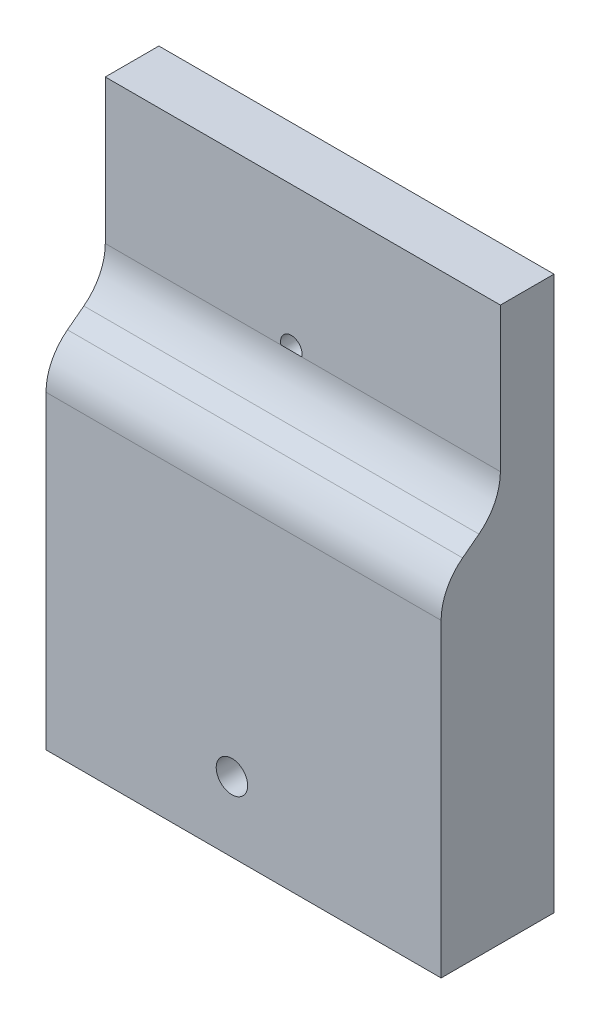
SolidWorks part; units mm, degrees
ref_plane "Front Plane" through (0, 0, 0) normal (0, 0, 1) x (1, 0, 0)
ref_plane "Top Plane" through (0, 0, 0) normal (0, 1, 0) x (1, 0, 0)
ref_plane "Right Plane" through (0, 0, 0) normal (1, 0, 0) x (0, 0, -1)
sketch "Sketch1" plane through (0, 0, 0) normal (0, 0, 1) x (1, 0, 0)
  line L1 (-110.6575, 3.089) -> (-47.1575, 3.089)
  line L2 (-110.6575, 3.089) -> (-110.6575, 91.989)
  line L3 (-110.6575, 91.989) -> (-47.1575, 91.989)
  line L4 (-47.1575, 3.089) -> (-47.1575, 91.989)
  dimension "D1" = 88.9
  dimension "D2" = 63.5
extrude "Boss-Extrude1" add sketch "Sketch1" along normal up to surface (18.1387 mm away)
sketch "Sketch2" plane through (-110.6575, 0, 0) normal (-1, 0, 0) x (0, 0, 1)
  line L0 (8.6137, 74.0185) -> (8.6137, 69.2433) construction
  line L1 (8.6137, 69.2433) -> (8.6137, 68.8056) construction
  line L2 (12.0626, 61.8377) -> (13.078, 61.0633) construction
  line L3 (13.078, 61.0633) -> (13.6744, 60.6085) construction
  line L4 (13.6744, 60.6085) -> (14.6898, 59.834) construction
  line L5 (18.1387, 14.3158) -> (18.1387, 52.8662) construction
  line L6 (8.6137, 74.0185) -> (8.6137, 69.2433)
  line L7 (8.6137, 69.2433) -> (8.6137, 68.8056)
  line L8 (12.0626, 61.8377) -> (13.078, 61.0633)
  line L9 (13.078, 61.0633) -> (13.6744, 60.6085)
  line L10 (13.6744, 60.6085) -> (14.6898, 59.834)
  line L11 (18.1387, 14.3158) -> (18.1387, 52.8662)
  line L12 (8.6137, 74.0185) -> (8.6137, 91.989)
  line L13 (18.1387, 91.989) -> (0, 91.989) construction
  line L14 (8.6137, 91.989) -> (18.1387, 91.989)
  line L15 (18.1387, 91.989) -> (18.1387, 52.8662)
  arc A0 (8.6358, 68.1839) -> (12.0626, 61.8377) centre (17.3767, 68.8056) ccw construction
  arc A1 (8.6137, 68.8056) -> (8.6358, 68.1839) centre (17.3767, 68.8056) ccw construction
  arc A2 (18.1166, 53.4879) -> (14.6898, 59.834) centre (9.3757, 52.8662) ccw construction
  arc A3 (18.1387, 52.8662) -> (18.1166, 53.4879) centre (9.3757, 52.8662) ccw construction
  arc A4 (8.6358, 68.1839) -> (12.0626, 61.8377) centre (17.3767, 68.8056) ccw
  arc A5 (8.6137, 68.8056) -> (8.6358, 68.1839) centre (17.3767, 68.8056) ccw
  arc A6 (18.1166, 53.4879) -> (14.6898, 59.834) centre (9.3757, 52.8662) ccw
  arc A7 (18.1387, 52.8662) -> (18.1166, 53.4879) centre (9.3757, 52.8662) ccw
extrude "Cut-Extrude1" cut sketch "Sketch2" against normal up to surface (63.5 mm away) contours A7 L12 L6 L7 A5 A4 L8 L9 L10 A6 M2 M3 up to face at (-47.1575, 47.539, 9.0693)
sketch3d "Sketch_MAC1-1_PART1_MILLING" [suppressed]
  line L0 (-47.1575, 3.089, 18.1387) -> (-47.1575, 13.089, 18.1387)
  line L1 (-47.1575, 3.089, 18.1387) -> (-57.1575, 3.089, 18.1387)
  point P0 (-47.1575, 3.089, 18.1387)
  point P1 (-47.1575, 13.089, 18.1387)
  point P2 (-57.1575, 3.089, 18.1387)
sketch3d "Stock_PART1_MILLING"
  line L12 (-47.1575, 3.089, 0) -> (-47.1575, 91.989, 0)
  line L13 (-47.1575, 91.989, 0) -> (-110.6575, 91.989, 0)
  line L14 (-110.6575, 91.989, 0) -> (-110.6575, 3.089, 0)
  line L15 (-110.6575, 3.089, 0) -> (-47.1575, 3.089, 0)
  line L16 (-47.1575, 3.089, 18.1387) -> (-47.1575, 91.989, 18.1387)
  line L17 (-47.1575, 91.989, 18.1387) -> (-110.6575, 91.989, 18.1387)
  line L18 (-110.6575, 91.989, 18.1387) -> (-110.6575, 3.089, 18.1387)
  line L19 (-110.6575, 3.089, 18.1387) -> (-47.1575, 3.089, 18.1387)
  line L20 (-47.1575, 3.089, 0) -> (-47.1575, 3.089, 18.1387)
  line L21 (-47.1575, 91.989, 0) -> (-47.1575, 91.989, 18.1387)
  line L22 (-110.6575, 91.989, 0) -> (-110.6575, 91.989, 18.1387)
  line L23 (-110.6575, 3.089, 0) -> (-110.6575, 3.089, 18.1387)
  point P35 (-47.1575, 47.539, 0)
  point P36 (-78.9075, 91.989, 0)
  point P37 (-110.6575, 47.539, 0)
  point P38 (-78.9075, 3.089, 0)
  point P39 (-47.1575, 47.539, 18.1387)
  point P40 (-78.9075, 91.989, 18.1387)
  point P41 (-110.6575, 47.539, 18.1387)
  point P42 (-78.9075, 3.089, 18.1387)
  point P43 (-47.1575, 3.089, 9.0693)
  point P44 (-47.1575, 91.989, 9.0693)
  point P45 (-110.6575, 91.989, 9.0693)
  point P46 (-110.6575, 3.089, 9.0693)
  point P47 (-78.9075, 47.539, 9.0693)
  point P48 (-47.1575, 47.539, 9.0693)
  point P49 (-78.9075, 47.539, 18.1387)
  point P50 (-110.6575, 47.539, 9.0693)
  point P51 (-78.9075, 47.539, 0)
  point P52 (-78.9075, 3.089, 9.0693)
  point P53 (-78.9075, 91.989, 9.0693)
hole_wizard "#29 (0.136) Diameter Hole1" positions "Sketch6" profile "Sketch5" hole size "#29" standard "ANSI Inch"
sketch "Sketch6" plane through (0, 0, 8.6137) normal (0, 0, 1) x (1, 0, 0)
  arc A0 (-79.0939, 68.8056) -> (-82.4355, 68.8056) centre (-80.7647, 69.2433) ccw construction
  point P0 (-80.7647, 69.2433)
sketch "Sketch5" plane through (-80.7647, 69.2433, 8.6137) normal (1, 0, 0) x (0, -1, 0)
  line L0 (0, 0) -> (0, 8.6137)
  line L1 (0, 8.6137) -> (1.7272, 8.6137)
  line L2 (1.7272, 8.6137) -> (1.7272, 0)
  line L5 (1.7272, 0) -> (0, 0)
  line L11 (0, -6.35) -> (0, 107.95) construction
  dimension "Thru Hole Dia." = 3.4544
  dimension "Thru Hole Depth" = 8.6137
hole_wizard "#8 (0.199) Diameter Hole1" positions "Sketch8" profile "Sketch7" hole size "#8" standard "ANSI Inch" end condition through all
sketch "Sketch8" plane through (0, 0, 18.1387) normal (0, 0, 1) x (1, 0, 0)
  point P0 (-80.7774, 14.3158)
sketch "Sketch7" plane through (-80.7774, 14.3158, 18.1387) normal (1, 0, 0) x (0, -1, 0)
  line L0 (0, 0) -> (0, 18.1387)
  line L1 (0, 18.1387) -> (2.5273, 18.1387)
  line L2 (2.5273, 18.1387) -> (2.5273, 0)
  line L5 (2.5273, 0) -> (0, 0)
  line L11 (0, -6.35) -> (0, 107.95) construction
  dimension "Thru Hole Dia." = 5.0546
  dimension "Thru Hole Depth" = 18.1387
sketch "Sketch9" plane through (0, 0, 18.1387) normal (0, 0, 1) x (1, 0, 0)
  line L0 (-110.6575, 91.989) -> (-110.6575, 3.089) construction
  line L1 (-110.6575, 37.222) -> (-47.1575, 37.222)
  line L2 (-110.6575, 37.222) -> (-110.6575, 91.989)
  line L3 (-110.6575, 91.989) -> (-47.1575, 91.989)
  line L4 (-47.1575, 37.222) -> (-47.1575, 91.989)
